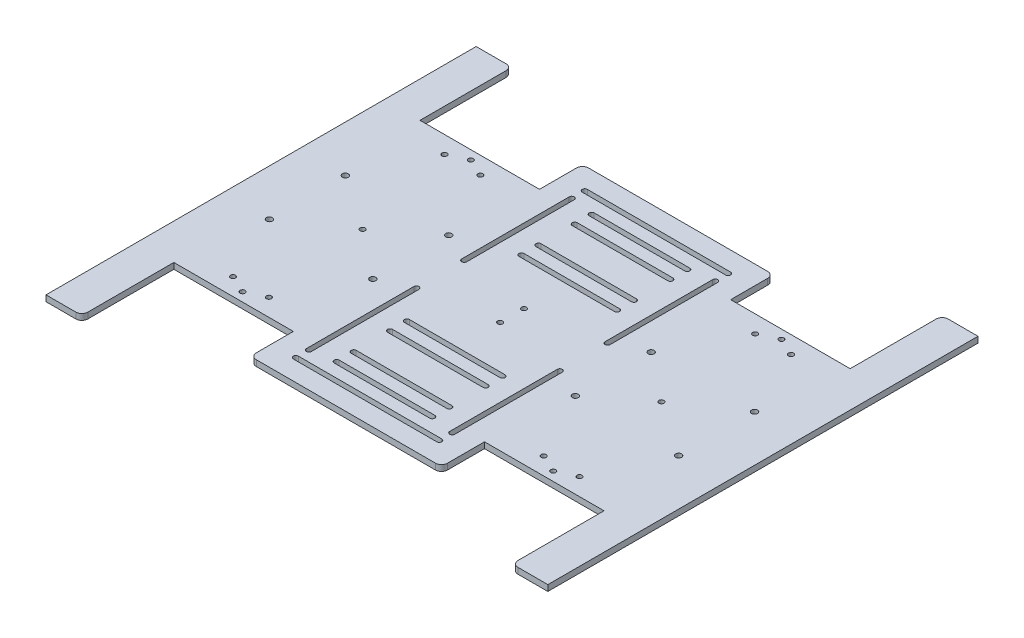
SolidWorks part; units mm, degrees
ref_plane "前视基准面" through (0, 0, 0) normal (0, 0, 1) x (1, 0, 0)
ref_plane "上视基准面" through (0, 0, 0) normal (0, 1, 0) x (1, 0, 0)
ref_plane "右视基准面" through (0, 0, 0) normal (1, 0, 0) x (0, 0, -1)
sketch "草图1" plane through (0, 0, 0) normal (0, 1, 0) x (1, 0, 0)
  line L0 (-180, 180) -> (-180, 103)
  line L1 (-210, -180) -> (-180, -180)
  line L2 (-210, -180) -> (-210, 180)
  line L3 (-210, 180) -> (-180, 180)
  line L4 (210, -180) -> (210, 180)
  line L5 (-210, -180) -> (210, 180) construction
  line L6 (-210, 180) -> (210, -180) construction
  line L7 (-180, 103) -> (-80, 103)
  line L8 (-80, 103) -> (-80, 180)
  line L9 (180, 180) -> (210, 180)
  line L10 (0, -14) -> (0, 14) construction
  line L11 (-210, 0) -> (210, 0) construction
  line L12 (-180, -180) -> (-180, -103)
  line L13 (-180, -103) -> (-80, -103)
  line L14 (-80, -103) -> (-80, -180)
  line L15 (80, -103) -> (80, -180)
  line L16 (180, -180) -> (180, -103)
  line L17 (180, -103) -> (80, -103)
  line L18 (180, 180) -> (180, 103)
  line L19 (180, 103) -> (80, 103)
  line L20 (80, 103) -> (80, 180)
  line L21 (-80, 180) -> (80, 180)
  line L22 (-80, -180) -> (80, -180)
  line L23 (180, -180) -> (210, -180)
  point P0 (0, 0)
  dimension "D1" = 420
  dimension "D2" = 360
  dimension "D3" = 100
  dimension "D4" = 77
  dimension "D5" = 30
extrude "凸台-拉伸1" add sketch "草图1" along normal blind 5
sketch "草图2" plane through (0, 5, 0) normal (0, 1, 0) x (1, 0, 0)
  line L0 (130, -103) -> (130, -89.161) construction
  line L1 (80, -103) -> (180, -103) construction
  line L2 (145, -88.5) -> (115, -88.5) construction
  line L3 (0, -180) -> (0, 180) construction
  line L4 (-80, -180) -> (80, -180) construction
  line L5 (80, 180) -> (-80, 180) construction
  line L6 (210, 0) -> (-210, 0) construction
  line L7 (210, -180) -> (210, 180) construction
  line L8 (-210, 180) -> (-210, -180) construction
  line L9 (145, 88.5) -> (115, 88.5) construction
  line L10 (130, 103) -> (130, 89.161) construction
  line L11 (-130, 103) -> (-130, 89.161) construction
  line L12 (-145, 88.5) -> (-115, 88.5) construction
  line L13 (-145, -88.5) -> (-115, -88.5) construction
  line L14 (-130, -103) -> (-130, -89.161) construction
  circle A0 centre (115, -88.5) radius 2.1
  circle A1 centre (145, -88.5) radius 2.1
  circle A2 centre (130, -95.5) radius 2.1
  circle A3 centre (130, 95.5) radius 2.1
  circle A4 centre (145, 88.5) radius 2.1
  circle A5 centre (115, 88.5) radius 2.1
  circle A6 centre (-115, 88.5) radius 2.1
  circle A7 centre (-145, 88.5) radius 2.1
  circle A8 centre (-130, 95.5) radius 2.1
  circle A9 centre (-130, -95.5) radius 2.1
  circle A10 centre (-145, -88.5) radius 2.1
  circle A11 centre (-115, -88.5) radius 2.1
  point P10 (130, -88.5)
  dimension "D1" = 4.2
  dimension "D2" = 30
  dimension "D3" = 7
  dimension "D4" = 7.5
extrude "切除-拉伸1" cut sketch "草图2" against normal through all
fillet "圆角1" radius 5 8 edges at (-180, 2.5, -180) (180, 2.5, 180) (80, 2.5, 180) (-180, 2.5, 180) (-80, 2.5, 180) (-80, 2.5, -180) (180, 2.5, -180) (80, 2.5, -180)
sketch "草图3" plane through (0, 0, 0) normal (0, -1, 0) x (1, 0, 0)
  line L0 (84.75, 31.75) -> (84.75, -31.75) construction
  line L2 (80, 175) -> (80, 103) construction
  line L3 (80, 103) -> (80, -103) construction
  line L4 (80, 0) -> (210, 0) construction
  line L5 (210, 180) -> (210, -180) construction
  line L6 (171.25, 31.75) -> (171.25, -31.75) construction
  line L7 (171.25, 31.75) -> (84.75, 31.75) construction
  line L8 (171.25, -31.75) -> (84.75, -31.75) construction
  line L9 (0, 180) -> (0, -180) construction
  line L10 (-75, 180) -> (75, 180) construction
  line L11 (75, -180) -> (-75, -180) construction
  line L12 (-171.25, -31.75) -> (-84.75, -31.75) construction
  line L13 (-171.25, 31.75) -> (-84.75, 31.75) construction
  line L14 (-171.25, 31.75) -> (-171.25, -31.75) construction
  line L15 (-84.75, 31.75) -> (-84.75, -31.75) construction
  circle A0 centre (84.75, 31.75) radius 2.5
  circle A1 centre (84.75, -31.75) radius 2.5
  circle A2 centre (171.25, 31.75) radius 2.5
  circle A3 centre (171.25, -31.75) radius 2.5
  circle A4 centre (-171.25, -31.75) radius 2.5
  circle A5 centre (-171.25, 31.75) radius 2.5
  circle A6 centre (-84.75, -31.75) radius 2.5
  circle A7 centre (-84.75, 31.75) radius 2.5
  point P8 (84.75, 0)
  dimension "D1" = 63.5
  dimension "D2" = 5
  dimension "D3" = 5
  dimension "D5" = 5
  dimension "D6" = 86.5
  dimension "D7" = 5
  dimension "D4" = 4.75
extrude "切除-拉伸2" cut sketch "草图3" against normal through all
sketch "草图4" plane through (0, 0, 0) normal (0, -1, 0) x (1, 0, 0)
  line L0 (-125, 0) -> (125, 0) construction
  line L1 (0, 10) -> (0, -10) construction
  circle A0 centre (-125, 0) radius 2.1
  circle A1 centre (125, 0) radius 2.1
  circle A2 centre (0, 10) radius 2.1
  circle A3 centre (0, -10) radius 2.1
  dimension "D1" = 4.2
  dimension "D2" = 4.2
  dimension "D3" = 125
  dimension "D4" = 125
  dimension "D5" = 4.2
  dimension "D6" = 4.2
  dimension "D7" = 10
  dimension "D8" = 10
extrude "切除-拉伸3" cut sketch "草图4" against normal through all
sketch "草图5" plane through (0, 5, 0) normal (0, 1, 0) x (1, 0, 0)
  line L0 (-80, -139) -> (80, -139)
  line L1 (-80, -103) -> (-80, -175) construction
  line L2 (80, -175) -> (80, -103) construction
  line L3 (-80, -139) -> (-80, -205.8894)
  line L4 (80, 103) -> (80, 175) construction
  line L5 (80, 139) -> (-80, 139)
  line L6 (-80, 175) -> (-80, 103) construction
  line L7 (-80, -205.8894) -> (80, -205.8894)
  line L8 (80, -205.8894) -> (80, -139)
  line L9 (-80, 139) -> (-80, 214.5585)
  line L10 (-80, 214.5585) -> (80, 221.0602)
  line L11 (80, 221.0602) -> (80, 139)
extrude "切除-拉伸4" cut sketch "草图5" against normal through all
fillet "圆角2" radius 5 4 edges at (-80, 2.5, 139) (80, 2.5, 139) (80, 2.5, -139) (-80, 2.5, -139)
sketch "草图6" plane through (0, 5, 0) normal (0, 1, 0) x (1, 0, 0)
  line L0 (-60, 123) -> (60, 123)
  line L1 (0, -198.0238) -> (0, 198.0238) construction
  line L2 (60, 118.8) -> (-60, 118.8)
  line L3 (0, 0) -> (259.1086, 0) construction
  line L4 (-75, 139) -> (75, 139) construction
  line L5 (-40, 108.8) -> (40, 108.8)
  line L6 (40, 104.6) -> (-40, 104.6)
  line L7 (-62.1, 110) -> (-62.1, 20)
  line L8 (-40, 94.6) -> (40, 94.6)
  line L9 (40, 90.4) -> (-40, 90.4)
  line L10 (62.1, 110) -> (62.1, 20)
  line L11 (60, 20) -> (-60, 20) construction
  line L12 (57.9, 20) -> (57.9, 110)
  line L13 (-57.9, 110) -> (-57.9, 20)
  line L14 (-40, 64.2) -> (40, 64.2)
  line L15 (-40, 50) -> (40, 50)
  line L16 (40, 45.8) -> (-40, 45.8)
  line L17 (40, 60) -> (-40, 60)
  line L18 (60, -20) -> (-60, -20) construction
  line L19 (40, -60) -> (-40, -60)
  line L20 (40, -45.8) -> (-40, -45.8)
  line L21 (-40, -50) -> (40, -50)
  line L22 (-40, -64.2) -> (40, -64.2)
  line L23 (-57.9, -110) -> (-57.9, -20)
  line L24 (57.9, -20) -> (57.9, -110)
  line L25 (62.1, -110) -> (62.1, -20)
  line L26 (40, -90.4) -> (-40, -90.4)
  line L27 (-40, -94.6) -> (40, -94.6)
  line L28 (-62.1, -110) -> (-62.1, -20)
  line L29 (40, -104.6) -> (-40, -104.6)
  line L30 (-40, -108.8) -> (40, -108.8)
  line L31 (60, -118.8) -> (-60, -118.8)
  line L32 (-60, -123) -> (60, -123)
  arc A0 (-60, 123) -> (-60, 118.8) centre (-60, 120.9) ccw
  arc A1 (60, 118.8) -> (60, 123) centre (60, 120.9) ccw
  arc A2 (-40, 108.8) -> (-40, 104.6) centre (-40, 106.7) ccw
  arc A3 (40, 104.6) -> (40, 108.8) centre (40, 106.7) ccw
  arc A4 (-40, 94.6) -> (-40, 90.4) centre (-40, 92.5) ccw
  arc A5 (40, 90.4) -> (40, 94.6) centre (40, 92.5) ccw
  arc A6 (-57.9, 110) -> (-62.1, 110) centre (-60, 110) ccw
  arc A7 (62.1, 110) -> (57.9, 110) centre (60, 110) ccw
  arc A8 (-62.1, 20) -> (-57.9, 20) centre (-60, 20) ccw
  arc A9 (57.9, 20) -> (62.1, 20) centre (60, 20) ccw
  arc A11 (-40, 50) -> (-40, 45.8) centre (-40, 47.9) ccw
  arc A12 (40, 45.8) -> (40, 50) centre (40, 47.9) ccw
  arc A13 (-40, 64.2) -> (-40, 60) centre (-40, 62.1) ccw
  arc A14 (40, 60) -> (40, 64.2) centre (40, 62.1) ccw
  arc A15 (57.9, -20) -> (62.1, -20) centre (60, -20) cw
  arc A16 (-62.1, -20) -> (-57.9, -20) centre (-60, -20) cw
  arc A17 (40, -60) -> (40, -64.2) centre (40, -62.1) cw
  arc A18 (-40, -64.2) -> (-40, -60) centre (-40, -62.1) cw
  arc A19 (40, -45.8) -> (40, -50) centre (40, -47.9) cw
  arc A20 (-40, -50) -> (-40, -45.8) centre (-40, -47.9) cw
  arc A21 (62.1, -110) -> (57.9, -110) centre (60, -110) cw
  arc A22 (-57.9, -110) -> (-62.1, -110) centre (-60, -110) cw
  arc A23 (40, -90.4) -> (40, -94.6) centre (40, -92.5) cw
  arc A24 (-40, -94.6) -> (-40, -90.4) centre (-40, -92.5) cw
  arc A25 (40, -104.6) -> (40, -108.8) centre (40, -106.7) cw
  arc A26 (-40, -108.8) -> (-40, -104.6) centre (-40, -106.7) cw
  arc A27 (60, -118.8) -> (60, -123) centre (60, -120.9) cw
  arc A28 (-60, -123) -> (-60, -118.8) centre (-60, -120.9) cw
  circle A29 centre (0, 10) radius 2.1 construction
  point P20 (0, 104.6)
  point P29 (0, 90.4)
  point P31 (60, 9.9169)
  dimension "D1" = 2.1
  dimension "D4" = 60
  dimension "D9" = 2.1
  dimension "D12" = 60
  dimension "D13" = 60
  dimension "D15" = 2.1
  dimension "D17" = 40
  dimension "D19" = 2.1
  dimension "D21" = 40
  dimension "D2" = 16
  dimension "D3" = 120
  dimension "D5" = 10
  dimension "D6" = 80
  dimension "D7" = 80
  dimension "D8" = 10
  dimension "D10" = 90
  dimension "D11" = 90
  dimension "D14" = 80
  dimension "D16" = 30
  dimension "D18" = 80
  dimension "D20" = 10
  dimension "D22" = 10
extrude "切除-拉伸5" cut sketch "草图6" against normal through all
